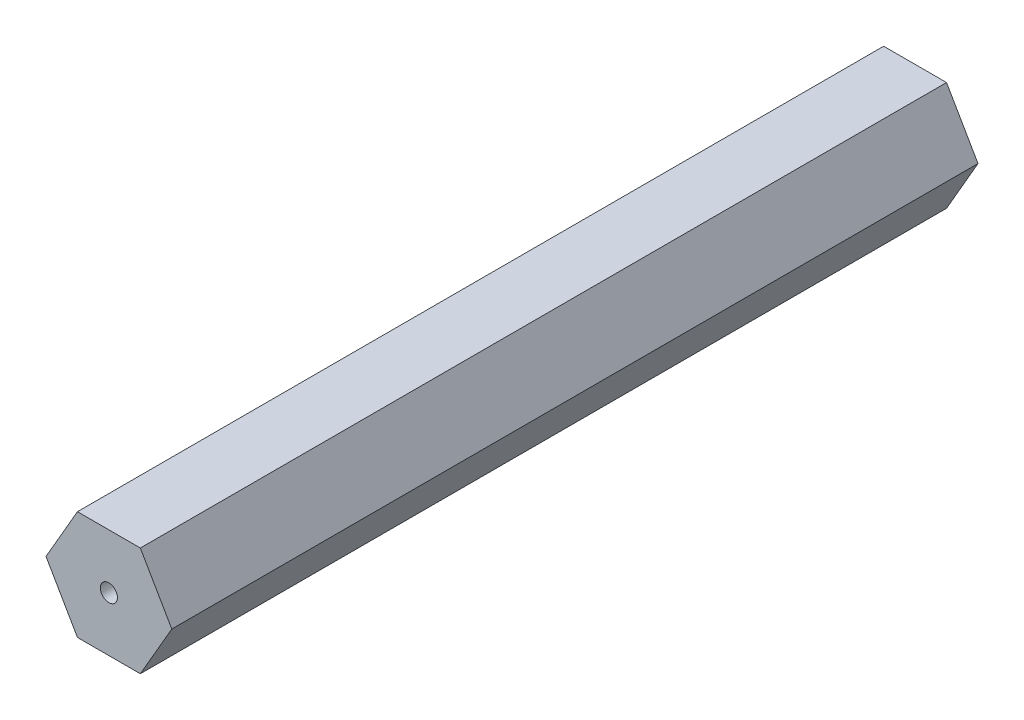
SolidWorks part; units mm, degrees
material "7075-T6 (SN)"
ref_plane "Front Plane" through (0, 0, 0) normal (0, 0, 1) x (1, 0, 0)
ref_plane "Top Plane" through (0, 0, 0) normal (0, 1, 0) x (1, 0, 0)
ref_plane "Right Plane" through (0, 0, 0) normal (1, 0, 0) x (0, 0, -1)
sketch "Sketch1" plane through (0, 0, 0) normal (0, 0, 1) x (1, 0, 0)
  line L1 (7.3323, 0) -> (3.6662, 6.35)
  line L2 (3.6662, 6.35) -> (-3.6662, 6.35)
  line L3 (-3.6662, 6.35) -> (-7.3323, 0)
  line L4 (-7.3323, 0) -> (-3.6662, -6.35)
  line L5 (-3.6662, -6.35) -> (3.6662, -6.35)
  line L6 (3.6662, -6.35) -> (7.3323, 0)
  circle A0 centre (0, 0) radius 6.35 construction
  dimension "D1" = 12.7
extrude "Boss-Extrude1" add sketch "Sketch1" along normal blind 94
sketch "Sketch2" plane through (0, 0, 94) normal (0, 0, 1) x (1, 0, 0)
  circle A0 centre (0, 0) radius 1
  dimension "D1" = 2
extrude "Cut-Extrude1" cut sketch "Sketch2" against normal through all
